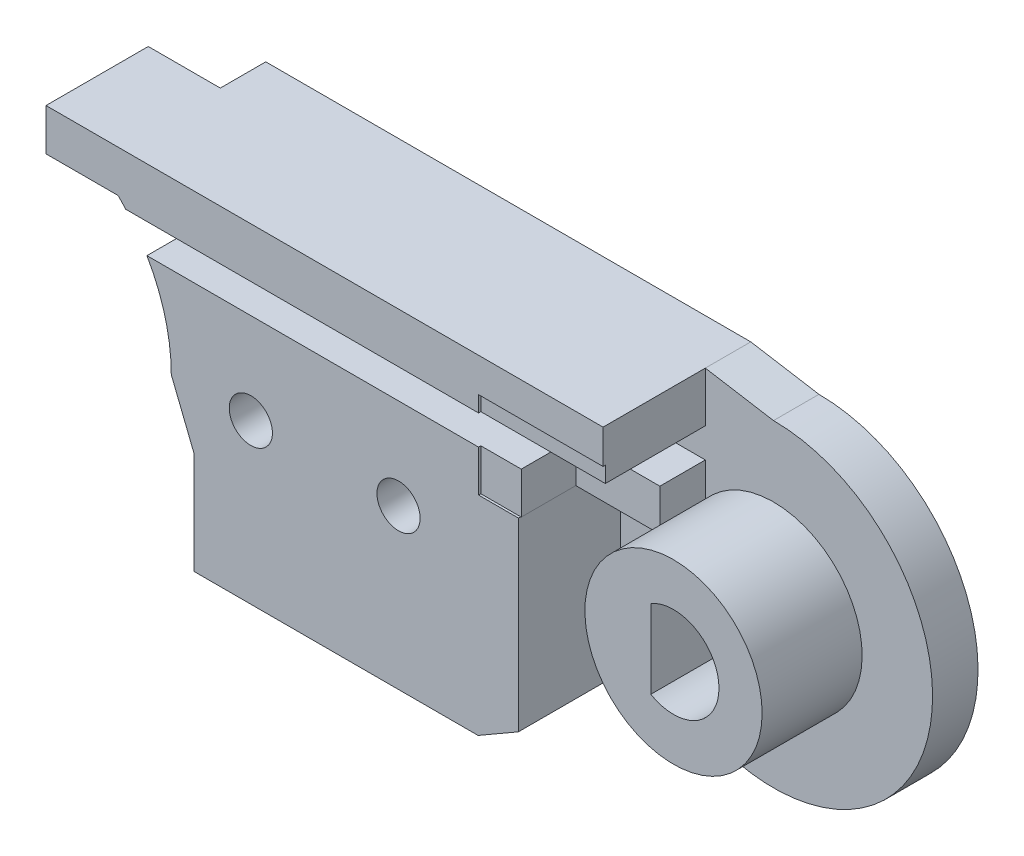
SolidWorks part; units mm, degrees
ref_plane "Front Plane" through (0, 0, 0) normal (0, 0, 1) x (1, 0, 0)
ref_plane "Top Plane" through (0, 0, 0) normal (0, 1, 0) x (1, 0, 0)
ref_plane "Right Plane" through (0, 0, 0) normal (1, 0, 0) x (0, 0, -1)
sketch "Sketch3" plane through (0, 0, 0) normal (0, 0, 1) x (1, 0, 0)
  line L7 (8, 0) -> (9, -2.5)
  line L11 (30, 7) -> (27, 7.5)
  line L13 (0, 7) -> (0, 7.5) construction
  line L14 (0, 7.5) -> (-22.3287, 7.5) construction
  line L15 (0, 5.3) -> (-14, 5.3) construction
  line L16 (0, 4) -> (-14, 4) construction
  line L17 (-14, 4) -> (-14, 5.3) construction
  line L18 (5.6569, 5.6569) -> (5.6569, 7.5)
  line L19 (5.6569, 7.5) -> (27, 7.5)
  line L20 (21.5, -7) -> (9, -7)
  line L21 (9, -7) -> (9, -2.5)
  line L23 (25.0503, -4.9497) -> (21.5, -7)
  arc A4 (8, 0) -> (5.6569, 5.6569) centre (0, 0) ccw
  arc A5 (25.0503, -4.9497) -> (30, 7) centre (30, 0) ccw
  circle A6 centre (0, 0) radius 7 construction
  circle A7 centre (0, 0) radius 3.9 construction
  circle A8 centre (0, 0) radius 5.3 construction
  circle A9 centre (0, 0) radius 4 construction
  dimension "D10" = 0.5
  dimension "D17" = 14
  dimension "D5" = 135
  dimension "D6" = 12.5
  dimension "D7" = 4.5
  dimension "D8" = 1
  dimension "D9" = 45
  dimension "D11" = 1.8431
  dimension "D12" = 30
  dimension "D14" = 3
extrude "Boss-Extrude1" add sketch "Sketch3" along normal blind 2 contours A5 L11 L19 L18 A4 L7 L21 L20 L23
sketch "Sketch20" plane through (0, 0, 0) normal (0, 0, 1) x (1, 0, 0)
  line L0 (0, 7) -> (0, 7.5) construction
  line L1 (0, 7.5) -> (-19.4737, 7.5) construction
  line L2 (0, 5.3) -> (-14, 5.3) construction
  line L3 (0, 4) -> (-14, 4) construction
  line L4 (-14, 4) -> (-14, 5.3) construction
  line L5 (0, 5.3) -> (17.4849, 5.3) construction
  line L6 (17.4849, 5.3) -> (17.4849, 4) construction
  line L7 (17.4849, 4) -> (0, 4) construction
  line L8 (-2.5, 7.5) -> (-2.5, 2.868) construction
  circle A0 centre (0, 0) radius 7 construction
  circle A1 centre (0, 0) radius 3.9 construction
  circle A3 centre (0, 0) radius 5.3 construction
  circle A4 centre (0, 0) radius 4 construction
  circle A5 centre (0, 0) radius 2 construction
  dimension "D1" = 0
  dimension "D2" = 2.5
ref_plane "Plane1" through (0, 0, 2) normal (0, 0, 1) x (1, 0, 0)
sketch "Sketch4" plane through (0, 0, 2) normal (0, 0, 1) x (1, 0, 0)
  line L4 (5.6569, 5.6569) -> (5.6569, 7.5)
  line L5 (5.6569, 5.6569) -> (5.6569, 7.5) construction
  line L6 (5.6569, 7.5) -> (21.5, 7.5)
  line L10 (8, 0) -> (9, -2.5)
  line L11 (9, -2.5) -> (9, -7)
  line L12 (9, -7) -> (21.5, -7)
  line L13 (21.5, -7) -> (21.5, 7.5)
  arc A0 (8, 0) -> (5.6569, 5.6569) centre (0, 0) ccw construction
  arc A3 (8, 0) -> (5.6569, 5.6569) centre (0, 0) ccw
sketch "Sketch22" plane through (0, 0, 2) normal (0, 0, 1) x (1, 0, 0)
  line L0 (5.6569, 5.6569) -> (2.4868, 5.6569)
  line L1 (5.6569, 7.5) -> (21.5, 7.5)
  line L2 (5.6569, 7.5) -> (2.4868, 7.5)
  line L3 (2.4868, 7.5) -> (2.4868, 5.6569)
  line L6 (8, 0) -> (9, -2.5)
  line L7 (9, -2.5) -> (9, -7)
  line L8 (9, -7) -> (21.5, -7)
  line L10 (21.5, 7.5) -> (27, 7.5)
  line L11 (27, 7.5) -> (27, 2.172)
  line L12 (27, 2.172) -> (23.2751, 2.172)
  line L13 (21.5, -7) -> (23.2751, -5.9749)
  line L14 (25.0503, -4.9497) -> (21.5, -7) construction
  line L15 (23.2751, -5.9749) -> (23.2751, 2.172)
  arc A0 (8, 0) -> (5.6569, 5.6569) centre (0, 0) ccw
extrude "Boss-Extrude6" add sketch "Sketch22" along normal blind 4.5
sketch "Sketch25" plane through (0, 0, 2) normal (0, 0, 1) x (1, 0, 0)
  line L0 (0, 5.3) -> (18.0981, 5.3) construction
  line L1 (0, 4) -> (18.0981, 4) construction
  line L2 (18.0981, 4) -> (18.0981, 5.3) construction
sketch "Sketch26" plane through (0, 0, 2) normal (0, 0, 1) x (1, 0, 0)
  line L1 (18.0981, 5.3) -> (2.5301, 5.3)
  line L2 (18.0981, 4) -> (2.5301, 4)
  line L3 (2.5301, 5.3) -> (2.5301, 4)
  line L4 (18.0981, 5.3) -> (27, 5.3)
  line L5 (27, 2.172) -> (27, 7.5) construction
  line L6 (27, 5.3) -> (27, 4)
  line L7 (27, 4) -> (18.0981, 4)
extrude "Cut-Extrude6" cut sketch "Sketch26" along normal blind 4.5
ref_plane "Plane18" through (0, 0, 6.5) normal (0, 0, 1) x (1, 0, 0)
sketch "Sketch31" plane through (0, 0, 6.5) normal (0, 0, 1) x (1, 0, 0)
  line L0 (2.4327, 5.6569) -> (0, 5.6569)
  line L4 (9, -5.6569) -> (0, -5.6569)
  line L5 (2.4327, 5.6569) -> (2.4868, 7.5)
  line L12 (9, -7) -> (9, -5.6569)
  line L13 (9, -2.5) -> (9, -7) construction
  line L16 (27, 7.5) -> (27, 2.172)
  line L17 (27, 2.172) -> (23.2751, 2.172)
  line L18 (23.2751, -5.9749) -> (23.2751, 2.172)
  line L19 (27, 7.5) -> (2.4868, 7.5)
  line L20 (9, -7) -> (21.5, -7)
  line L21 (21.5, -7) -> (23.2751, -5.9749)
  arc A0 (0, 5.6569) -> (0, -5.6569) centre (0, 0) ccw
  dimension "D1" = 5.6569
extrude "Boss-Extrude14" add sketch "Sketch31" along normal blind 2.3 separate body
sketch "Sketch32" plane through (0, 0, 8.8) normal (0, 0, 1) x (1, 0, 0)
  circle A0 centre (0, 0) radius 2.1
extrude "Cut-Extrude7" cut sketch "Sketch32" against normal blind 2.3
sketch "Sketch33" plane through (0, 0, 8.8) normal (0, 0, 1) x (1, 0, 0)
  line L4 (9, -5.6569) -> (9, -7)
  line L11 (9, -7) -> (21.5, -7)
  line L15 (21.5, -7) -> (21.5, -5.6569)
  line L16 (21.5, -5.6569) -> (9, -5.6569)
  line L17 (2.4868, 7.5) -> (21.5, 7.5)
  line L18 (27, 7.5) -> (2.4868, 7.5) construction
  line L19 (2.4868, 7.5) -> (2.4327, 5.6569)
  line L20 (2.4327, 5.6569) -> (21.5, 5.6569)
  line L21 (21.5, 5.6569) -> (21.5, 7.5)
extrude "Boss-Extrude15" add sketch "Sketch33" along normal blind 1.2
sketch "Sketch34" plane through (0, 0, 2) normal (0, 0, 1) x (1, 0, 0)
  line L0 (30, 5.3) -> (18.0981, 5.3) construction
  line L1 (30, 4) -> (18.0981, 4) construction
  circle A0 centre (30, 0) radius 2 construction
  circle A1 centre (30, 0) radius 5.3 construction
  circle A2 centre (30, 0) radius 4 construction
sketch "Sketch35" plane through (0, 0, 8.8) normal (0, 0, 1) x (1, 0, 0)
  line L0 (27, 2.172) -> (27, 6)
  line L1 (27, 2.172) -> (21.5204, 2.172)
  line L2 (27, 6) -> (21.5204, 6)
  line L3 (21.5204, 2.172) -> (21.5204, 6)
  line L4 (27, 2.172) -> (27, 7.5) construction
extrude "Cut-Extrude8" cut sketch "Sketch35" against normal blind 2.4
sketch "Sketch36" plane through (0, 0, 6.4) normal (0, 0, 1) x (1, 0, 0)
  line L0 (27, 2.172) -> (27, 4)
  line L1 (27, 2.172) -> (23.3, 2.172)
  line L2 (27, 4) -> (23.3, 4)
  line L3 (23.3, 2.172) -> (23.3, 4)
  line L4 (21.5, -7) -> (21.5, 7.5) construction
  dimension "D1" = 1.8
extrude "Cut-Extrude9" cut sketch "Sketch36" against normal blind 2.4
sketch "Sketch37" plane through (0, 0, 2) normal (0, 0, 1) x (1, 0, 0)
  circle A0 centre (30, 0) radius 3.9
extrude "Boss-Extrude16" add sketch "Sketch37" along normal blind 4.4
sketch "Sketch39" plane through (0, 0, 6.4) normal (0, 0, 1) x (1, 0, 0)
  line L0 (29, 1.7321) -> (29, -1.7321)
  arc A0 (29, -1.7321) -> (29, 1.7321) centre (30, 0) ccw
  dimension "D2" = 4
  dimension "D1" = 1
extrude "Cut-Extrude10" cut sketch "Sketch39" against normal through all
sketch "Sketch43" plane through (0, 0, 8.8) normal (0, 0, 1) x (1, 0, 0)
  line L2 (0, -5.6569) -> (9, -5.6569) construction
  circle A0 centre (11.5, 0) radius 2.5
  circle A1 centre (18, 0) radius 2.5
  dimension "D1" = 2.5
  dimension "D3" = 5
  dimension "D4" = 6.5
  dimension "D2" = 5.6569
extrude "Boss-Extrude17" add sketch "Sketch43" along normal blind 1.2
sketch "Sketch44" plane through (0, 0, 10) normal (0, 0, 1) x (1, 0, 0)
  circle A0 centre (11.5, 0) radius 0.95
  circle A1 centre (18, 0) radius 0.95
  dimension "D1" = 1.9
  dimension "D2" = 1.9
extrude "Cut-Extrude11" cut sketch "Sketch44" against normal through all
sketch "Sketch45" plane through (0, 0, 0) normal (0, 0, -1) x (-1, 0, 0)
  circle A0 centre (-11.5, 0) radius 2
  circle A1 centre (-18, 0) radius 2
extrude "Cut-Extrude12" cut sketch "Sketch45" against normal blind 4.5
ref_plane "Plane17" through (0, 0, 10) normal (0, 0, 1) x (1, 0, 0)
sketch "Sketch48" plane through (0, 0, 2) normal (0, 0, 1) x (1, 0, 0)
  circle A0 centre (30, 0) radius 5 construction
sketch "Sketch51" plane through (0, 0, 10) normal (0, 0, 1) x (1, 0, 0)
  line L0 (18.2355, 5.6569) -> (27.0112, -4.8677) construction
  line L1 (2.4327, 5.6569) -> (21.5, 5.6569) construction
sketch "Sketch52" plane through (0, 5.6569, 0) normal (0, -1, 0) x (1, 0, 0)
  circle A0 centre (18.2355, 10) radius 0.75
extrude "Cut-Extrude13" cut sketch "Sketch52" along direction (0.6404, -0.768, 0) on the side against the normal blind 10
split "Split1" trim tools "Plane18" bodies to split 129 133 resulting bodies 134 135
delete or keep bodies "Body-Delete/Keep 1" type delete bodies bodies 135
